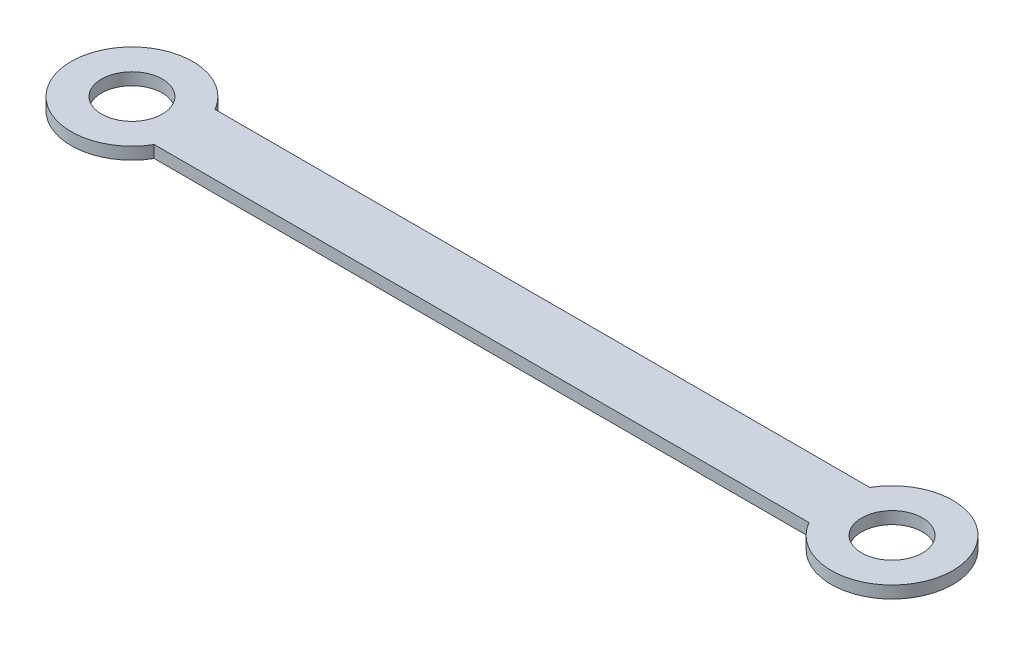
SolidWorks part; units mm, degrees
ref_plane "前基準面" through (0, 0, 0) normal (0, 0, 1) x (1, 0, 0)
ref_plane "上基準面" through (0, 0, 0) normal (0, 1, 0) x (1, 0, 0)
ref_plane "右基準面" through (0, 0, 0) normal (1, 0, 0) x (0, 0, -1)
sketch "草圖5" plane through (0, 0, 0) normal (0, 1, 0) x (1, 0, 0)
  line L0 (8.6603, -5) -> (116.3397, -5)
  line L2 (116.3397, 5) -> (8.6603, 5)
  circle A0 centre (0, 0) radius 5
  arc A1 (8.6603, 5) -> (8.6603, -5) centre (0, 0) ccw
  arc A2 (116.3397, -5) -> (116.3397, 5) centre (125, 0) ccw
  circle A3 centre (125, 0) radius 5
  dimension "D1" = 10
  dimension "D2" = 10
  dimension "D3" = 10
  dimension "D4" = 125
extrude "填料-伸長1" add sketch "草圖5" along normal blind 2
